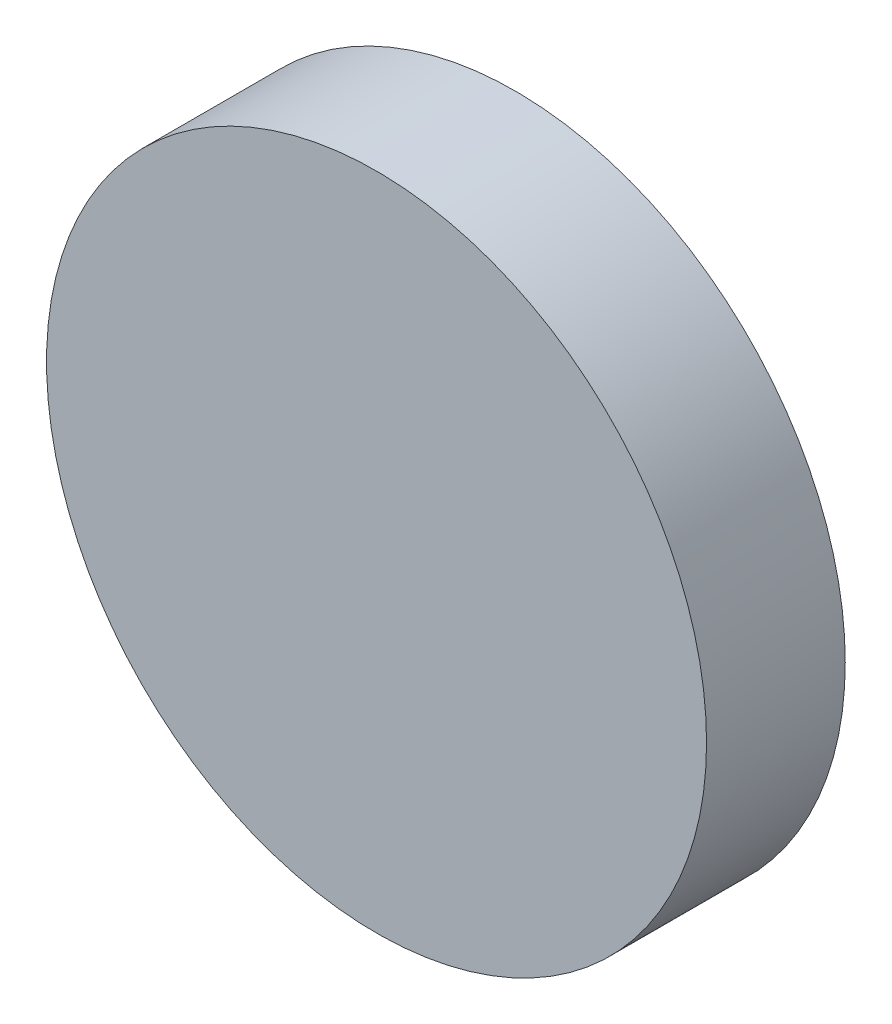
SolidWorks part; units mm, degrees
material "Boron"
ref_plane "Front" through (0, 0, 0) normal (0, 0, 1) x (1, 0, 0)
ref_plane "Top" through (0, 0, 0) normal (0, 1, 0) x (1, 0, 0)
ref_plane "Right" through (0, 0, 0) normal (1, 0, 0) x (0, 0, -1)
sketch "Sketch1" plane through (0, 0, 0) normal (0, 0, 1) x (1, 0, 0)
  circle A0 centre (0, 0) radius 128
extrude "Boss-Extrude1" add sketch "Sketch1" along normal blind 53.8
